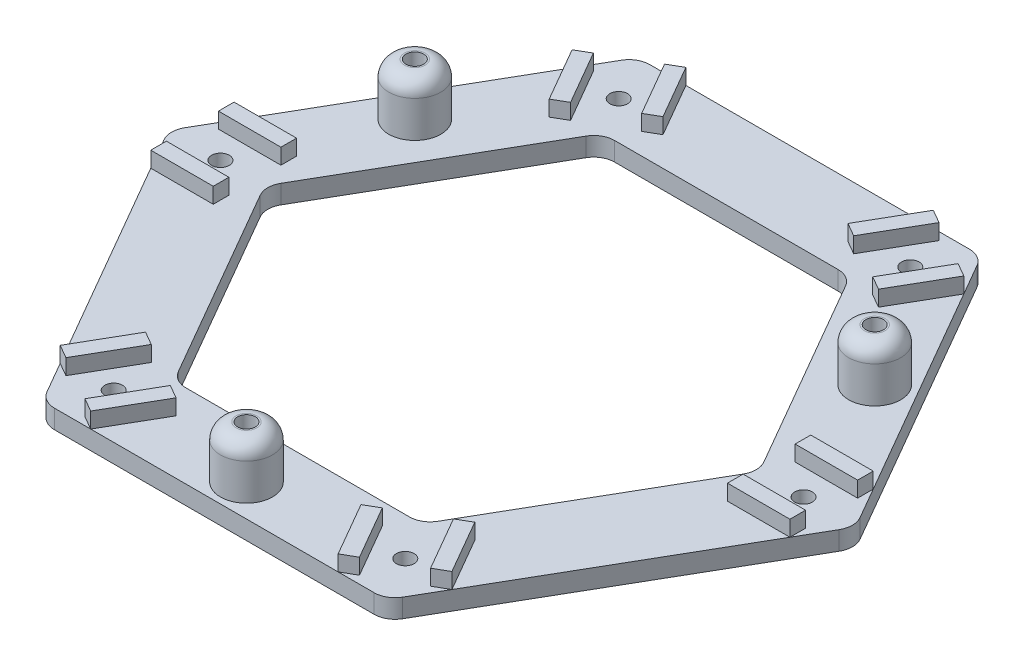
SolidWorks part; units mm, degrees
ref_plane "前视基准面" through (0, 0, 0) normal (0, 0, 1) x (1, 0, 0)
ref_plane "上视基准面" through (0, 0, 0) normal (0, 1, 0) x (1, 0, 0)
ref_plane "右视基准面" through (0, 0, 0) normal (1, 0, 0) x (0, 0, -1)
sketch "Sketch1" plane through (0, 0, 0) normal (0, 1, 0) x (1, 0, 0)
  line L0 (0, 38.2299) -> (0, 0) construction
  line L1 (33, 0) -> (16.5, 28.5788)
  line L2 (16.5, 28.5788) -> (-16.5, 28.5788)
  line L3 (-16.5, 28.5788) -> (-33, 0)
  line L4 (-33, 0) -> (-16.5, -28.5788)
  line L5 (-16.5, -28.5788) -> (16.5, -28.5788)
  line L6 (16.5, -28.5788) -> (33, 0)
  line L7 (0, 0) -> (-14, 24.2487) construction
  line L8 (0, 0) -> (-48.6795, 0) construction
  line L10 (11.8812, -20.5788) -> (23.7624, 0)
  line L11 (23.7624, 0) -> (11.8812, 20.5788)
  line L12 (11.8812, 20.5788) -> (-11.8812, 20.5788)
  line L13 (-11.8812, 20.5788) -> (-23.7624, 0)
  line L14 (-23.7624, 0) -> (-11.8812, -20.5788)
  line L15 (-11.8812, -20.5788) -> (11.8812, -20.5788)
  circle A0 centre (0, 0) radius 28.5788 construction
  circle A1 centre (-14, 24.2487) radius 0.85
  circle A2 centre (14, 24.2487) radius 0.85
  circle A3 centre (28, 0) radius 0.85
  circle A4 centre (14, -24.2487) radius 0.85
  circle A5 centre (0, 0) radius 20.5788 construction
  circle A6 centre (-14, -24.2487) radius 0.85
  circle A7 centre (-28, 0) radius 0.85
  point P17 (0, 0)
  dimension "D4" = 1.7
  dimension "D1" = 33
  dimension "D2" = 30
  dimension "D3" = 28
  dimension "D5" = 8
  dimension "D8" = 6
extrude "Extrude1" add sketch "Sketch1" along normal blind 1.8
fillet "Fillet1" radius 2 12 edges at (-16.5, 0.9, 28.5788) (16.5, 0.9, 28.5788) (16.5, 0.9, -28.5788) (-16.5, 0.9, -28.5788) (-11.8812, 0.9, 20.5788) (11.8812, 0.9, 20.5788) (11.8812, 0.9, -20.5788) (-11.8812, 0.9, -20.5788) (23.7624, 0.9, 0) (33, 0.9, 0) (-23.7624, 0.9, 0) (-33, 0.9, 0)
sketch "Sketch3" plane through (0, 1.8, 0) normal (0, 1, 0) x (1, 0, 0)
  line L0 (0, 31.5969) -> (0, 0) construction
  line L1 (0, 0) -> (-42.5258, 0) construction
  line L2 (0, 0) -> (-22.0836, 12.75) construction
  line L3 (-12.4585, 19.5788) -> (-23.185, 1) construction
  circle A0 centre (-22.0836, 12.75) radius 2.5
  circle A1 centre (22.0836, 12.75) radius 2.5
  circle A2 centre (0, -25.5) radius 2.5
  point P14 (0, 0)
  dimension "D1" = 5
  dimension "D2" = 25.5
  dimension "D3" = 3
extrude "Extrude3" add sketch "Sketch3" along normal blind 5
sketch "Sketch4" plane through (0, 1.8, 0) normal (0, 1, 0) x (1, 0, 0)
  circle A0 centre (-22.0836, 12.75) radius 0.85
  circle A1 centre (22.0836, 12.75) radius 0.85
  circle A2 centre (0, -25.5) radius 0.85
  dimension "D1" = 1.7
extrude "Extrude4" cut sketch "Sketch4" along normal through all and the other way blind 10
fillet "Fillet2" radius 1.5 3 edges at (0, 6.8, 28) (22.0836, 6.8, -10.25) (-22.0836, 6.8, -10.25)
sketch "草图1" plane through (0, 1.8, 0) normal (0, 1, 0) x (1, 0, 0)
  line L0 (0, 0) -> (-28, 0) construction
  line L1 (-30.6906, 4) -> (-24.6906, 4)
  line L2 (-30.6906, 4) -> (-30.6906, 2.5)
  line L3 (-30.6906, 2.5) -> (-24.6906, 2.5)
  line L4 (-24.6906, 4) -> (-24.6906, 2.5)
  line L5 (-17.0774, 27.5788) -> (-32.4226, 1) construction
  line L6 (-24.6906, -4) -> (-24.6906, -2.5)
  line L7 (-30.6906, -2.5) -> (-24.6906, -2.5)
  line L8 (-30.6906, -4) -> (-30.6906, -2.5)
  line L9 (-30.6906, -4) -> (-24.6906, -4)
  line L10 (-11.8812, 28.5788) -> (-8.8812, 23.3827)
  line L11 (-11.8812, 28.5788) -> (-13.1802, 27.8288)
  line L12 (-13.1802, 27.8288) -> (-10.1802, 22.6327)
  line L13 (-8.8812, 23.3827) -> (-10.1802, 22.6327)
  line L14 (-15.8094, 19.3827) -> (-14.5104, 20.1327)
  line L15 (-17.5104, 25.3288) -> (-14.5104, 20.1327)
  line L16 (-18.8094, 24.5788) -> (-17.5104, 25.3288)
  line L17 (-18.8094, 24.5788) -> (-15.8094, 19.3827)
  line L18 (18.8094, 24.5788) -> (15.8094, 19.3827)
  line L19 (18.8094, 24.5788) -> (17.5104, 25.3288)
  line L20 (17.5104, 25.3288) -> (14.5104, 20.1327)
  line L21 (15.8094, 19.3827) -> (14.5104, 20.1327)
  line L22 (8.8812, 23.3827) -> (10.1802, 22.6327)
  line L23 (13.1802, 27.8288) -> (10.1802, 22.6327)
  line L24 (11.8812, 28.5788) -> (13.1802, 27.8288)
  line L25 (11.8812, 28.5788) -> (8.8812, 23.3827)
  line L26 (30.6906, -4) -> (24.6906, -4)
  line L27 (30.6906, -4) -> (30.6906, -2.5)
  line L28 (30.6906, -2.5) -> (24.6906, -2.5)
  line L29 (24.6906, -4) -> (24.6906, -2.5)
  line L30 (24.6906, 4) -> (24.6906, 2.5)
  line L31 (30.6906, 2.5) -> (24.6906, 2.5)
  line L32 (30.6906, 4) -> (30.6906, 2.5)
  line L33 (30.6906, 4) -> (24.6906, 4)
  line L34 (11.8812, -28.5788) -> (8.8812, -23.3827)
  line L35 (11.8812, -28.5788) -> (13.1802, -27.8288)
  line L36 (13.1802, -27.8288) -> (10.1802, -22.6327)
  line L37 (8.8812, -23.3827) -> (10.1802, -22.6327)
  line L38 (15.8094, -19.3827) -> (14.5104, -20.1327)
  line L39 (17.5104, -25.3288) -> (14.5104, -20.1327)
  line L40 (18.8094, -24.5788) -> (17.5104, -25.3288)
  line L41 (18.8094, -24.5788) -> (15.8094, -19.3827)
  line L42 (-18.8094, -24.5788) -> (-15.8094, -19.3827)
  line L43 (-18.8094, -24.5788) -> (-17.5104, -25.3288)
  line L44 (-17.5104, -25.3288) -> (-14.5104, -20.1327)
  line L45 (-15.8094, -19.3827) -> (-14.5104, -20.1327)
  line L46 (-8.8812, -23.3827) -> (-10.1802, -22.6327)
  line L47 (-13.1802, -27.8288) -> (-10.1802, -22.6327)
  line L48 (-11.8812, -28.5788) -> (-13.1802, -27.8288)
  line L49 (-11.8812, -28.5788) -> (-8.8812, -23.3827)
  point P56 (0, 0)
  dimension "D1" = 1.5
  dimension "D2" = 6
  dimension "D3" = 5
  dimension "D4" = 6
extrude "凸台-拉伸1" add sketch "草图1" along normal blind 1.5
